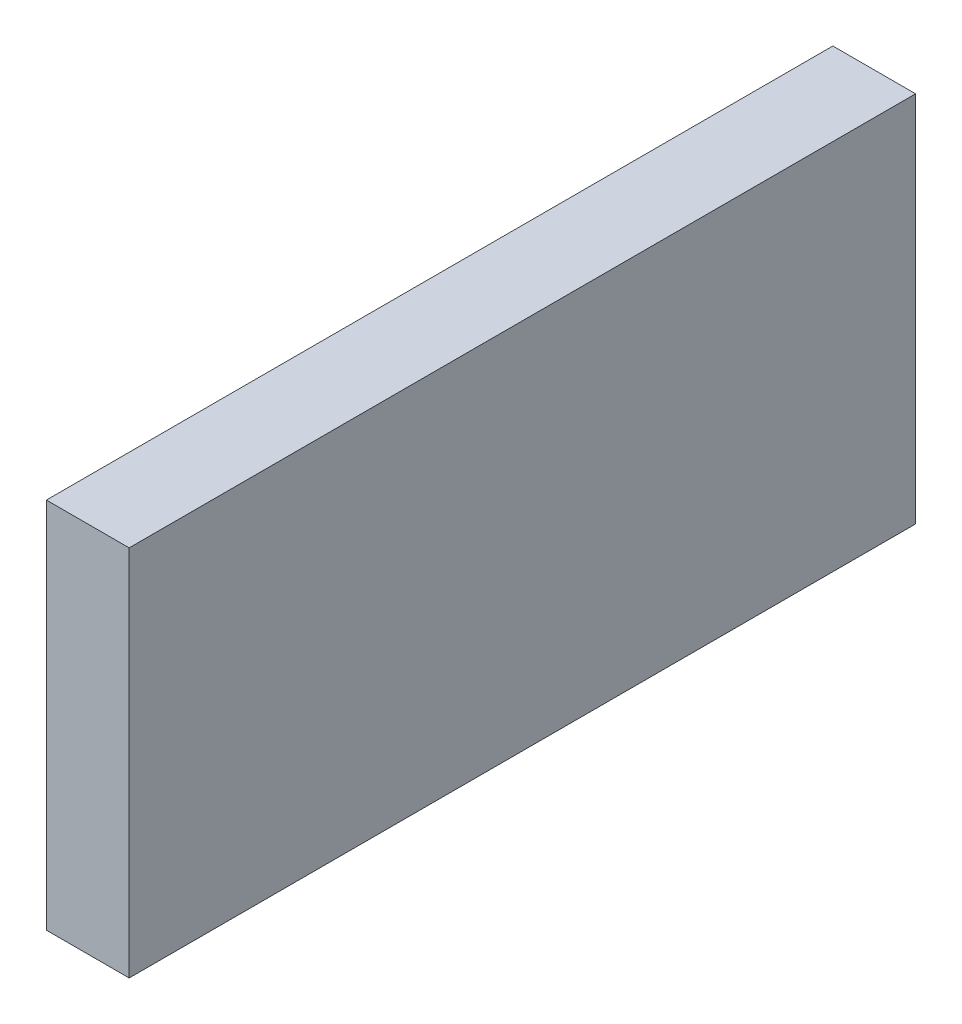
SolidWorks part; units mm, degrees
ref_plane "Front Plane" through (0, 0, 0) normal (0, 0, 1) x (1, 0, 0)
ref_plane "Top Plane" through (0, 0, 0) normal (0, 1, 0) x (1, 0, 0)
ref_plane "Right Plane" through (0, 0, 0) normal (1, 0, 0) x (0, 0, -1)
imported_body "Tower Pro MG90S Micro servo.STEP<1>"
sketch "Sketch1" plane through (16.1, 0, 0) normal (1, 0, 0) x (0, 0, -1)
  line L0 (-5.45, 9.375) -> (-5.45, 7.125) construction
  line L1 (-5.45, 9.375) -> (-0.7, 9.375)
  line L2 (-5.45, 9.375) -> (-5.45, 7.125)
  line L3 (-5.45, 7.125) -> (-0.7, 7.125)
  line L4 (-0.7, 9.375) -> (-0.7, 7.125)
  line L5 (-0.7, 9.375) -> (-5.45, 9.375) construction
extrude "Boss-Extrude1" add sketch "Sketch1" against normal blind 0.5
